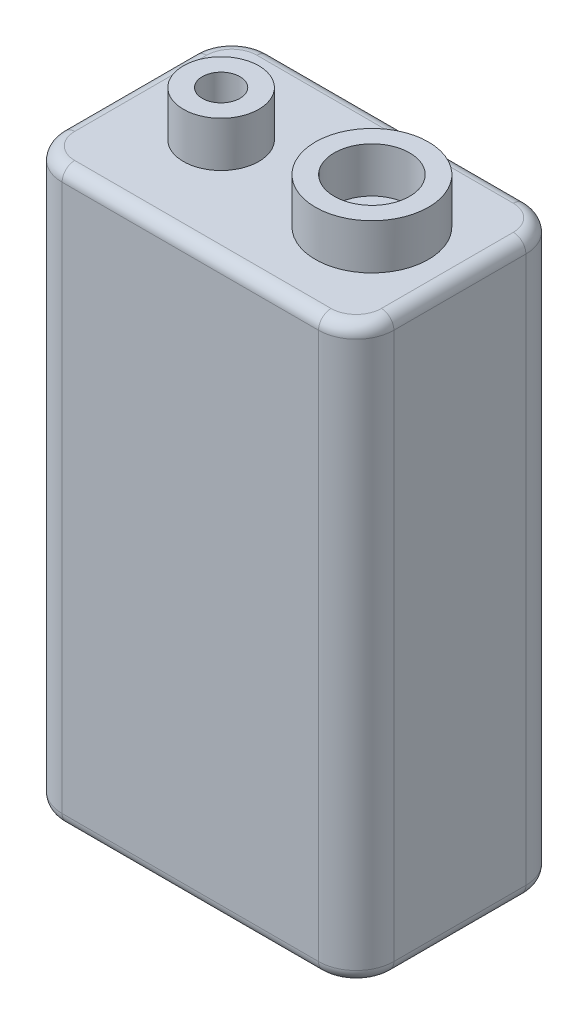
SolidWorks part; units mm, degrees
ref_plane "前基準面" through (0, 0, 0) normal (0, 0, 1) x (1, 0, 0)
ref_plane "上基準面" through (0, 0, 0) normal (0, 1, 0) x (1, 0, 0)
ref_plane "右基準面" through (0, 0, 0) normal (1, 0, 0) x (0, 0, -1)
sketch "草圖1" plane through (0, 0, 0) normal (0, 0, 1) x (1, 0, 0)
  line L1 (0, 0) -> (26.4, 0)
  line L2 (0, 0) -> (0, 45.5)
  line L3 (0, 45.5) -> (26.4, 45.5)
  line L4 (26.4, 0) -> (26.4, 45.5)
  dimension "D1" = 26.4
  dimension "D2" = 45.5
extrude "填料-伸長1" add sketch "草圖1" along normal blind 16.5
fillet "圓角1" radius 3 4 edges at (0, 22.75, 0) (0, 22.75, 16.5) (26.4, 22.75, 0) (26.4, 22.75, 16.5)
sketch "草圖2" plane through (0, 45.5, 0) normal (0, 1, 0) x (1, 0, 0)
  line L0 (7.4, -8.25) -> (19.4, -8.25) construction
  line L1 (19.4, -8.25) -> (26.4, -8.25) construction
  line L2 (26.4, -13.5) -> (26.4, -3) construction
  line L3 (0, -13.5) -> (0, -3) construction
  circle A0 centre (7.4, -8.25) radius 3
  circle A1 centre (19.4, -8.25) radius 4.5
  circle A2 centre (7.4, -8.25) radius 1.5
  circle A3 centre (19.4, -8.25) radius 3
  dimension "D1" = 6
  dimension "D2" = 9
  dimension "D3" = 1.5
  dimension "D4" = 1.5
  dimension "D6" = 7.4
  dimension "D5" = 12
  dimension "D7" = 7
extrude "填料-伸長2" add sketch "草圖2" along normal blind 3.6
fillet "圓角2" radius 1 16 edges at (25.5213, 45.5, 15.6213) (26.4, 45.5, 8.25) (25.5213, 45.5, 0.8787) (13.2, 45.5, 0) (0.8787, 45.5, 0.8787) (0, 45.5, 8.25) (0.8787, 45.5, 15.6213) (0.8787, 0, 15.6213) (13.2, 0, 16.5) (25.5213, 0, 15.6213) (26.4, 0, 8.25) (25.5213, 0, 0.8787) (13.2, 0, 0) (0.8787, 0, 0.8787) (0, 0, 8.25) (13.2, 45.5, 16.5)
